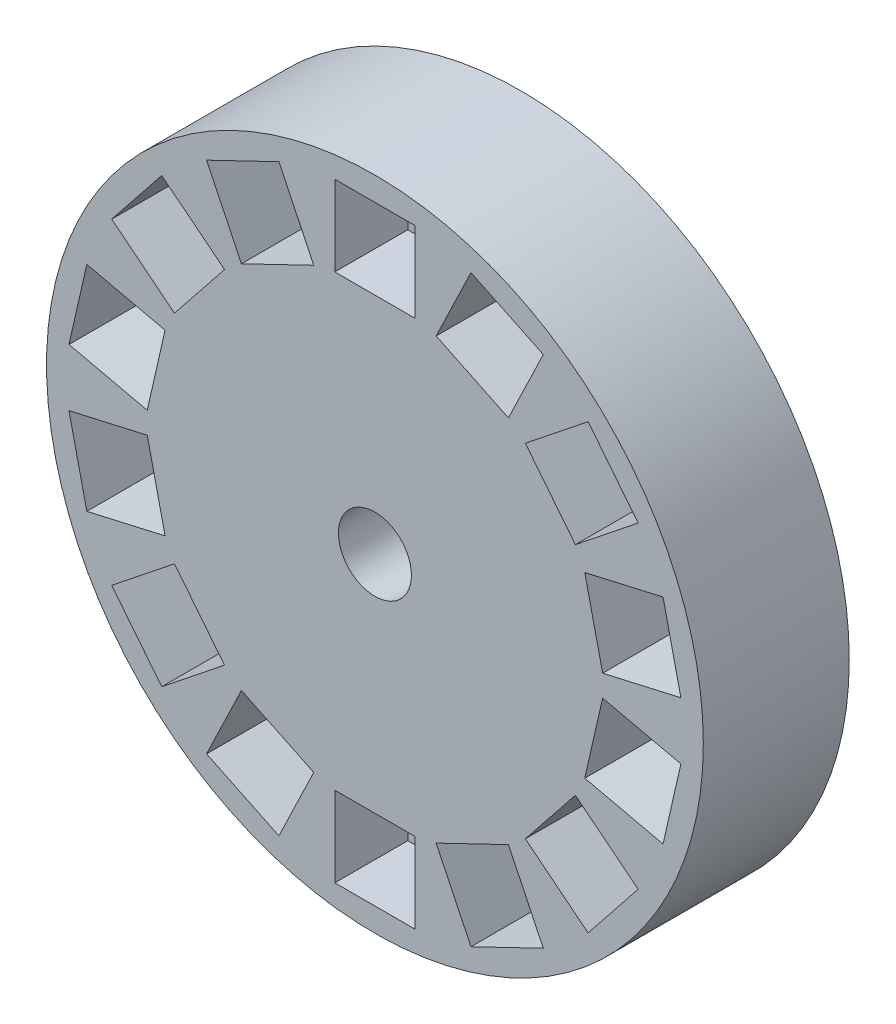
SolidWorks part; units mm, degrees
ref_plane "Płaszczyzna przednia" through (0, 0, 0) normal (0, 0, 1) x (1, 0, 0)
ref_plane "Płaszczyzna górna" through (0, 0, 0) normal (0, 1, 0) x (1, 0, 0)
ref_plane "Płaszczyzna prawa" through (0, 0, 0) normal (1, 0, 0) x (0, 0, -1)
sketch "Szkic1" plane through (0, 0, 0) normal (0, 0, 1) x (1, 0, 0)
  circle A0 centre (0, 0) radius 4.5
  circle A1 centre (0, 0) radius 0.5
extrude "Dodanie-wyciągnięcie1" add sketch "Szkic1" along normal blind 2
sketch "Szkic2" plane through (0, 0, 2) normal (0, 0, 1) x (1, 0, 0)
  line L0 (1.3159, 4.0002) -> (0.8387, 3.0091)
  line L1 (-0.55, 4.175) -> (0.55, 4.175)
  line L2 (-0.55, 4.175) -> (-0.55, 3.075)
  line L3 (-0.55, 3.075) -> (0.55, 3.075)
  line L4 (0.55, 4.175) -> (0.55, 3.075)
  line L5 (-0.55, 4.175) -> (0.55, 3.075) construction
  line L6 (-0.55, 3.075) -> (0.55, 4.175) construction
  line L7 (1.3159, 4.0002) -> (2.307, 3.5229)
  line L8 (2.307, 3.5229) -> (1.8297, 2.5318)
  line L9 (0.8387, 3.0091) -> (1.8297, 2.5318)
  line L10 (2.9212, 3.0331) -> (2.0612, 2.3472)
  line L11 (2.9212, 3.0331) -> (3.6071, 2.1731)
  line L12 (3.6071, 2.1731) -> (2.7471, 1.4872)
  line L13 (2.0612, 2.3472) -> (2.7471, 1.4872)
  line L14 (3.9479, 1.4652) -> (2.8755, 1.2205)
  line L15 (3.9479, 1.4652) -> (4.1927, 0.3928)
  line L16 (4.1927, 0.3928) -> (3.1203, 0.148)
  line L17 (2.8755, 1.2205) -> (3.1203, 0.148)
  line L18 (4.1927, -0.3928) -> (3.1203, -0.148)
  line L19 (4.1927, -0.3928) -> (3.9479, -1.4652)
  line L20 (3.9479, -1.4652) -> (2.8755, -1.2205)
  line L21 (3.1203, -0.148) -> (2.8755, -1.2205)
  line L22 (3.6071, -2.1731) -> (2.7471, -1.4872)
  line L23 (3.6071, -2.1731) -> (2.9212, -3.0331)
  line L24 (2.9212, -3.0331) -> (2.0612, -2.3472)
  line L25 (2.7471, -1.4872) -> (2.0612, -2.3472)
  line L26 (2.307, -3.5229) -> (1.8297, -2.5318)
  line L27 (2.307, -3.5229) -> (1.3159, -4.0002)
  line L28 (1.3159, -4.0002) -> (0.8387, -3.0091)
  line L29 (1.8297, -2.5318) -> (0.8387, -3.0091)
  line L30 (0.55, -4.175) -> (0.55, -3.075)
  line L31 (0.55, -4.175) -> (-0.55, -4.175)
  line L32 (-0.55, -4.175) -> (-0.55, -3.075)
  line L33 (0.55, -3.075) -> (-0.55, -3.075)
  line L34 (-1.3159, -4.0002) -> (-0.8387, -3.0091)
  line L35 (-1.3159, -4.0002) -> (-2.307, -3.5229)
  line L36 (-2.307, -3.5229) -> (-1.8297, -2.5318)
  line L37 (-0.8387, -3.0091) -> (-1.8297, -2.5318)
  line L38 (-2.9212, -3.0331) -> (-2.0612, -2.3472)
  line L39 (-2.9212, -3.0331) -> (-3.6071, -2.1731)
  line L40 (-3.6071, -2.1731) -> (-2.7471, -1.4872)
  line L41 (-2.0612, -2.3472) -> (-2.7471, -1.4872)
  line L42 (-3.9479, -1.4652) -> (-2.8755, -1.2205)
  line L43 (-3.9479, -1.4652) -> (-4.1927, -0.3928)
  line L44 (-4.1927, -0.3928) -> (-3.1203, -0.148)
  line L45 (-2.8755, -1.2205) -> (-3.1203, -0.148)
  line L46 (-4.1927, 0.3928) -> (-3.1203, 0.148)
  line L47 (-4.1927, 0.3928) -> (-3.9479, 1.4652)
  line L48 (-3.9479, 1.4652) -> (-2.8755, 1.2205)
  line L49 (-3.1203, 0.148) -> (-2.8755, 1.2205)
  line L50 (-3.6071, 2.1731) -> (-2.7471, 1.4872)
  line L51 (-3.6071, 2.1731) -> (-2.9212, 3.0331)
  line L52 (-2.9212, 3.0331) -> (-2.0612, 2.3472)
  line L53 (-2.7471, 1.4872) -> (-2.0612, 2.3472)
  line L54 (-2.307, 3.5229) -> (-1.8297, 2.5318)
  line L55 (-2.307, 3.5229) -> (-1.3159, 4.0002)
  line L56 (-1.3159, 4.0002) -> (-0.8387, 3.0091)
  line L57 (-1.8297, 2.5318) -> (-0.8387, 3.0091)
  point P0 (0, 3.625)
  point P61 (0, 0)
  dimension "D1" = 1.1
  dimension "D2" = 1.1
  dimension "D3" = 3.625
  dimension "D4" = 14
extrude "Wytnij-wyciągnięcie1" cut sketch "Szkic2" against normal blind 1
